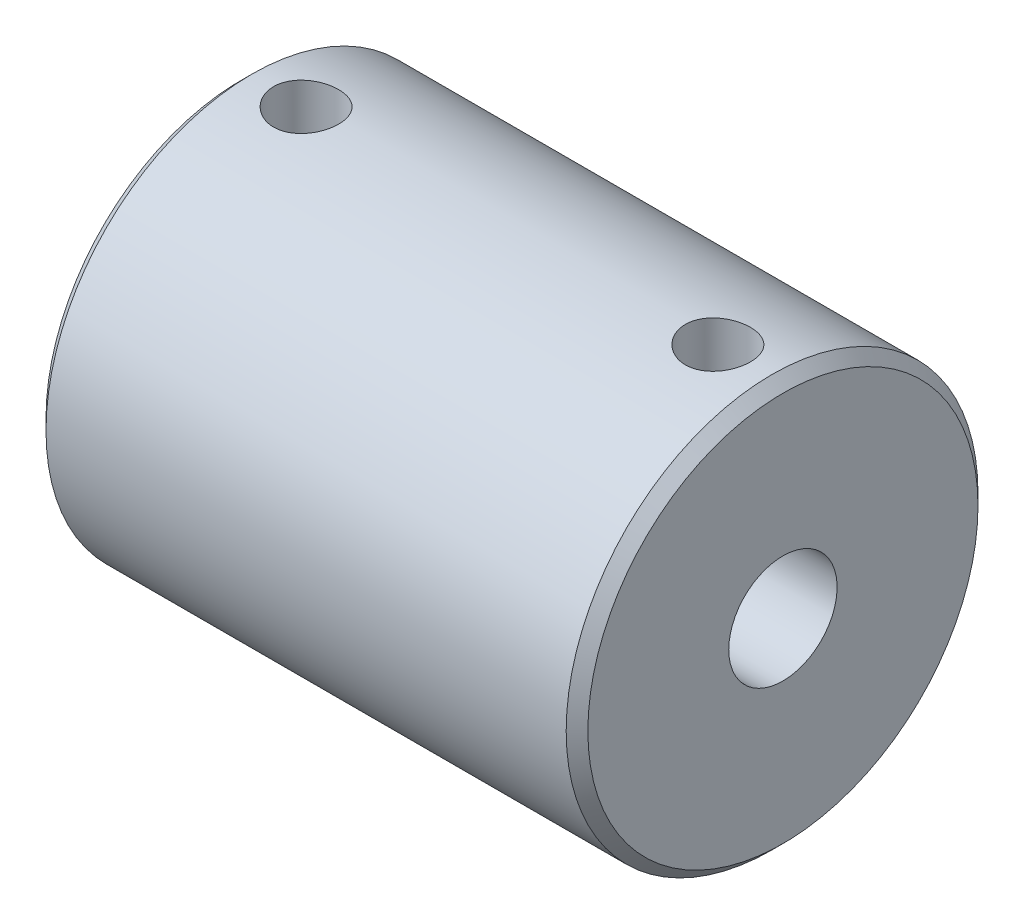
SolidWorks part; units mm, degrees
ref_plane "Front Plane" through (0, 0, 0) normal (0, 0, 1) x (1, 0, 0)
ref_plane "Top Plane" through (0, 0, 0) normal (0, 1, 0) x (1, 0, 0)
ref_plane "Right Plane" through (0, 0, 0) normal (1, 0, 0) x (0, 0, -1)
sketch "Sketch1" plane through (0, 0, 0) normal (0, 0, 1) x (1, 0, 0)
  line L0 (-12.5, 9.5) -> (12.5, 9.5)
  line L1 (-12.5, 4) -> (0, 4)
  line L2 (0, 2.5) -> (12.5, 2.5)
  line L3 (-12.5, 9.5) -> (-12.5, 4)
  line L4 (12.5, 9.5) -> (12.5, 2.5)
  line L5 (12.5, 9.5) -> (12.5, 2.5)
  line L6 (-12.5, 0) -> (12.5, 0) construction
  line L7 (960.4304, 0) -> (-960.4304, 0) construction
  line L8 (0, 4) -> (0, 2.5)
revolve "Revolve1" add sketch "Sketch1" angle 360 about L6
sketch "Sketch2" plane through (0, 0, 0) normal (0, 1, 0) x (1, 0, 0)
  circle A0 centre (-9.5, 0) radius 1.5
  circle A1 centre (9.5, 0) radius 1.5
extrude "Cut-Extrude1" cut sketch "Sketch2" along normal up to next
chamfer "Chamfer1" distance 0.5 angle 45 2 edges at (-12.5, 0, 9.5) (12.5, 0, 9.5)
